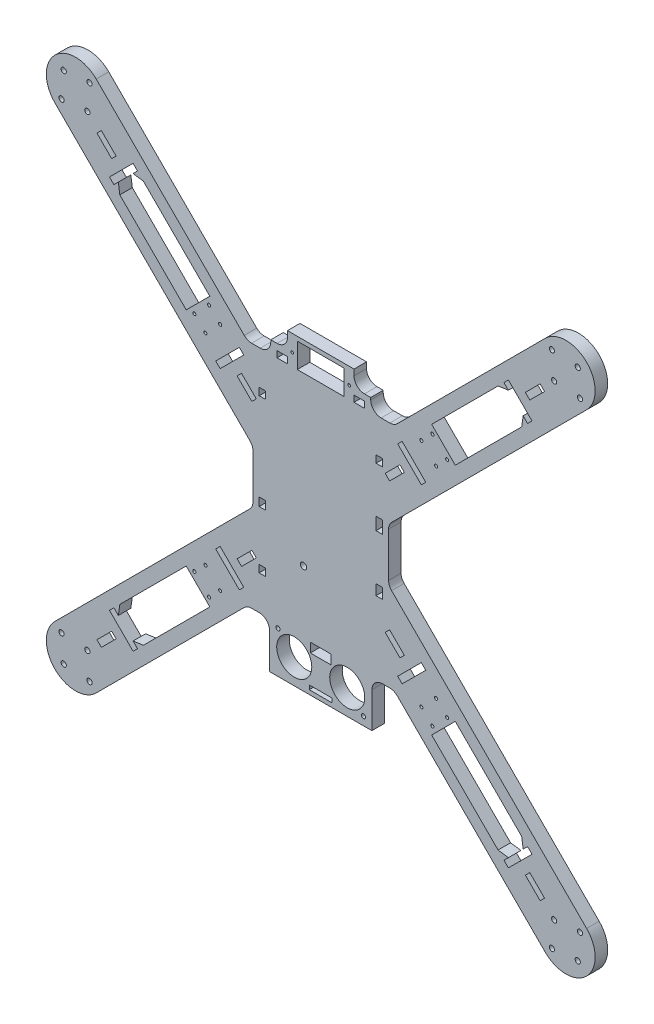
SolidWorks part; units mm, degrees
material "Custom Plastic"
ref_plane "Front Plane" through (0, 0, 0) normal (0, 0, 1) x (1, 0, 0)
ref_plane "Top Plane" through (0, 0, 0) normal (0, 1, 0) x (1, 0, 0)
ref_plane "Right Plane" through (0, 0, 0) normal (1, 0, 0) x (0, 0, -1)
sketch "Sketch1" plane through (0, 0, 0) normal (0, 0, 1) x (1, 0, 0)
  line L0 (117.5, 117.5) -> (-117.5, 117.5) construction
  line L1 (-117.5, 117.5) -> (117.5, -117.5) construction
  line L2 (117.5, -117.5) -> (-117.5, -117.5) construction
  line L3 (-117.5, -117.5) -> (117.5, 117.5) construction
  line L4 (117.5, 117.5) -> (117.5, -117.5) construction
  line L5 (-117.5, 117.5) -> (-117.5, -117.5) construction
  line L6 (0, 117.5) -> (0, -117.5) construction
  line L7 (35.201, 55) -> (15.95, 55)
  line L8 (-32.5, 55) -> (32.5, 55) construction
  line L9 (-35.201, 55) -> (-107.6005, 127.3995)
  line L10 (-127.3995, 107.6005) -> (-32.5, 12.701)
  line L11 (-117.5, 0) -> (117.5, 0) construction
  line L12 (-32.5, 12.701) -> (-32.5, -12.701)
  line L13 (32.5, 55) -> (32.5, -55) construction
  line L14 (32.5, -55) -> (-32.5, -55) construction
  line L15 (-32.5, -55) -> (-32.5, 55) construction
  line L16 (32.5, 55) -> (-32.5, -55) construction
  line L17 (-24.5, -55) -> (-24.5, -77)
  line L18 (-127.3995, -107.6005) -> (-32.5, -12.701)
  line L19 (-24.5, -77) -> (24.5, -77)
  line L20 (-35.201, -55) -> (-107.6005, -127.3995)
  line L21 (35.201, -55) -> (24.5, -55)
  line L22 (35.201, -55) -> (107.6005, -127.3995)
  line L23 (127.3995, -107.6005) -> (32.5, -12.701)
  line L24 (32.5, 12.701) -> (32.5, -12.701)
  line L25 (127.3995, 107.6005) -> (32.5, 12.701)
  line L26 (35.201, 55) -> (107.6005, 127.3995)
  line L27 (24.5, -55) -> (24.5, -77)
  line L28 (-24.5, -55) -> (-35.201, -55)
  line L29 (-15.95, 55) -> (-15.95, 68.8)
  line L30 (-15.95, 68.8) -> (15.95, 68.8)
  line L31 (15.95, 55) -> (15.95, 68.8)
  line L32 (-15.95, 55) -> (-35.201, 55)
  arc A0 (-107.6005, 127.3995) -> (-127.3995, 107.6005) centre (-117.5, 117.5) ccw
  arc A12 (-107.6005, -127.3995) -> (-127.3995, -107.6005) centre (-117.5, -117.5) cw
  arc A16 (107.6005, -127.3995) -> (127.3995, -107.6005) centre (117.5, -117.5) ccw
  arc A24 (107.6005, 127.3995) -> (127.3995, 107.6005) centre (117.5, 117.5) cw
  point P3 (0, 0)
  point P18 (0, 0)
  point P21 (0, -77)
  point P26 (0, 68.8)
  point P33 (-117.5, 117.5)
  point P34 (-32.5, 0)
  point P65 (0, -55)
  point P80 (0, 55)
  dimension "D3" = 14
  dimension "D8" = 24.5
  dimension "D7" = 22
  dimension "D1" = 235
  dimension "D2" = 235
  dimension "D4" = 65
  dimension "D5" = 110
  dimension "D6" = 28
  dimension "D9" = 13.8
  dimension "D10" = 31.9
extrude "Boss-Extrude1" add sketch "Sketch1" against normal blind 6
sketch "Sketch4" plane through (0, 0, 0) normal (0, 0, 1) x (1, 0, 0)
  line L0 (0, 0) -> (0, 55) construction
  line L2 (0, 0) -> (-32.5, 0) construction
  line L3 (-32.5, 12.701) -> (-32.5, -12.701) construction
  line L4 (-32.5, 0) -> (-32.5, 12.701) construction
  line L5 (-32.5, 12.701) -> (-127.3995, 107.6005) construction
  line L6 (-35.201, 55) -> (-107.6005, 127.3995) construction
  line L7 (-107.6005, 127.3995) -> (-127.3995, 107.6005) construction
  line L8 (-110.7825, 124.2175) -> (-124.2175, 110.7825) construction
  line L9 (-123.1569, 123.1569) -> (-111.8431, 111.8431) construction
  circle A20 centre (-110.7825, 124.2175) radius 1.25
  circle A21 centre (-124.2175, 110.7825) radius 1.25
  circle A22 centre (-123.1569, 123.1569) radius 1.25
  circle A23 centre (-111.8431, 111.8431) radius 1.25
  circle A24 centre (111.8431, 111.8431) radius 1.25
  circle A25 centre (110.7825, 124.2175) radius 1.25
  circle A26 centre (123.1569, 123.1569) radius 1.25
  circle A27 centre (124.2175, 110.7825) radius 1.25
  circle A28 centre (111.8431, -111.8431) radius 1.25
  circle A29 centre (124.2175, -110.7825) radius 1.25
  circle A30 centre (123.1569, -123.1569) radius 1.25
  circle A31 centre (110.7825, -124.2175) radius 1.25
  circle A32 centre (-111.8431, -111.8431) radius 1.25
  circle A33 centre (-110.7825, -124.2175) radius 1.25
  circle A34 centre (-123.1569, -123.1569) radius 1.25
  circle A35 centre (-124.2175, -110.7825) radius 1.25
  point P16 (-117.5, 117.5)
  point P19 (-117.5, 117.5)
  point P26 (-117.5, 117.5)
  point P62 (0, 0)
  dimension "D1" = 55
  dimension "D4" = 2.5
  dimension "D2" = 19
  dimension "D5" = 35.201
  dimension "D3" = 16
extrude "Cut-Extrude1" cut sketch "Sketch4" against normal through all
sketch "Sketch5" plane through (0, 0, 0) normal (0, 0, 1) x (1, 0, 0)
  line L4 (0, 0) -> (0, 14.0392) construction
  line L6 (15.95, 68.8) -> (-15.95, 68.8) construction
  line L7 (-11.25, 66.8) -> (-11.25, 55)
  line L8 (-11.25, 55) -> (11.25, 55)
  line L9 (11.25, 55) -> (11.25, 66.8)
  line L10 (11.25, 66.8) -> (-11.25, 66.8)
  line L12 (0, 66.8) -> (0, 55) construction
  line L13 (-13.65, 60.9) -> (13.65, 60.9) construction
  circle A2 centre (-13.65, 60.9) radius 0.65
  circle A3 centre (13.65, 60.9) radius 0.65
  point P20 (0, 60.9)
  point P21 (0, 60.9)
  dimension "D8" = 1.3
  dimension "D9" = 1.3
  dimension "D2" = 2
  dimension "D10" = 27.3
  dimension "D11" = 22.5
  dimension "D12" = 11.8
extrude "Cut-Extrude2" cut sketch "Sketch5" against normal through all
sketch "Sketch6" plane through (0, 0, 0) normal (0, 0, 1) x (1, 0, 0)
  line L1 (-11.25, 55) -> (11.25, 55) construction
  circle A0 centre (-8.25, -25) radius 1.5
  dimension "D3" = 3
  dimension "D1" = 80
  dimension "D2" = 3
extrude "Cut-Extrude3" cut sketch "Sketch6" against normal through all
sketch "Sketch7" plane through (0, 0, 0) normal (0, 0, 1) x (1, 0, 0)
  line L0 (-22.5, -55) -> (-22.5, -75) construction
  line L5 (-22.5, -75) -> (22.5, -75) construction
  line L6 (22.5, -75) -> (22.5, -55) construction
  line L7 (22.5, -55) -> (-22.5, -55) construction
  line L8 (0, -55) -> (0, -75) construction
  line L9 (-12.7, -65) -> (0, -65) construction
  line L10 (-24.5, -77) -> (24.5, -77) construction
  line L11 (-24.5, -55) -> (-24.5, -77) construction
  line L12 (-5, -55) -> (-5, -59.5)
  line L13 (-5, -59.5) -> (5, -59.5)
  line L15 (5, -55) -> (-5, -55)
  line L16 (-5.5, -75) -> (-5.5, -73)
  line L17 (-5.5, -73) -> (5.5, -73)
  line L21 (5.5, -75) -> (-5.5, -75)
  line L22 (5, -55) -> (5, -59.5)
  line L23 (5.5, -75) -> (5.5, -73)
  circle A5 centre (-20.5, -57) radius 1
  circle A6 centre (-12.7, -65) radius 8.4
  circle A7 centre (12.7, -65) radius 8.4
  circle A8 centre (20.5, -73) radius 1
  point P25 (0, -59.5)
  point P26 (0, -73)
  dimension "D3" = 2
  dimension "D6" = 20
  dimension "D13" = 5.5
  dimension "D5" = 45
  dimension "D1" = 2
  dimension "D4" = 16.8
  dimension "D14" = 2
  dimension "D2" = 2
  dimension "D7" = 2
  dimension "D8" = 2
  dimension "D9" = 12.7
  dimension "D10" = 5
  dimension "D11" = 4.5
  dimension "D12" = 2
  dimension "D15" = 2
  dimension "D16" = 2
extrude "Cut-Extrude4" cut sketch "Sketch7" against normal through all
sketch "Sketch8" plane through (0, 0, 0) normal (0, 0, 1) x (1, 0, 0)
  line L0 (101.2365, -89.9228) -> (89.9228, -101.2365)
  line L1 (89.9228, -101.2365) -> (87.8015, -99.1152)
  line L2 (36.8898, -48.2035) -> (48.2035, -36.8898)
  line L3 (48.2035, -36.8898) -> (50.3249, -39.0111)
  line L4 (105.4792, -85.6802) -> (85.6802, -105.4792) construction
  line L5 (127.3995, -107.6005) -> (32.5, -12.701) construction
  line L6 (35.201, -55) -> (107.6005, -127.3995) construction
  line L7 (40.0718, -37.9505) -> (37.9505, -40.0718)
  line L8 (115.8431, -107.8431) -> (111.8431, -111.8431) construction
  line L9 (37.9505, -40.0718) -> (30.8794, -33.0007)
  line L10 (50.3249, 39.0111) -> (48.2035, 36.8898)
  line L11 (30.8794, -33.0007) -> (33.0007, -30.8794)
  line L12 (33.0007, -30.8794) -> (40.0718, -37.9505)
  line L13 (42.5467, -42.5467) -> (39.0111, -39.0111) construction
  line L14 (35.201, -55) -> (107.6005, -127.3995) construction
  line L15 (100.1759, -98.0546) -> (98.0546, -100.1759)
  line L16 (98.0546, -100.1759) -> (105.1256, -107.247)
  line L17 (105.1256, -107.247) -> (107.247, -105.1256)
  line L18 (107.247, -105.1256) -> (100.1759, -98.0546)
  line L19 (99.1152, -99.1152) -> (95.5797, -95.5797) construction
  line L20 (-101.2365, -89.9228) -> (-99.1152, -87.8015)
  line L21 (-100.1759, -98.0546) -> (-107.247, -105.1256)
  line L22 (-107.247, -105.1256) -> (-105.1256, -107.247)
  line L23 (-105.1256, -107.247) -> (-98.0546, -100.1759)
  line L24 (-98.0546, -100.1759) -> (-100.1759, -98.0546)
  line L25 (-89.9228, -101.2365) -> (-101.2365, -89.9228)
  line L26 (-36.8898, -48.2035) -> (-39.0111, -50.3249)
  line L27 (-48.2035, -36.8898) -> (-36.8898, -48.2035)
  line L28 (-37.9505, -40.0718) -> (-40.0718, -37.9505)
  line L29 (-30.8794, -33.0007) -> (-37.9505, -40.0718)
  line L30 (-40.0718, -37.9505) -> (-33.0007, -30.8794)
  line L31 (-33.0007, -30.8794) -> (-30.8794, -33.0007)
  line L32 (-89.9228, 101.2365) -> (-87.8015, 99.1152)
  line L33 (-98.0546, 100.1759) -> (-105.1256, 107.247)
  line L34 (-105.1256, 107.247) -> (-107.247, 105.1256)
  line L35 (-107.247, 105.1256) -> (-100.1759, 98.0546)
  line L36 (-100.1759, 98.0546) -> (-98.0546, 100.1759)
  line L37 (-101.2365, 89.9228) -> (-89.9228, 101.2365)
  line L38 (-48.2035, 36.8898) -> (-50.3249, 39.0111)
  line L39 (-36.8898, 48.2035) -> (-48.2035, 36.8898)
  line L40 (-40.0718, 37.9505) -> (-37.9505, 40.0718)
  line L41 (-33.0007, 30.8794) -> (-40.0718, 37.9505)
  line L42 (-37.9505, 40.0718) -> (-30.8794, 33.0007)
  line L43 (-30.8794, 33.0007) -> (-33.0007, 30.8794)
  line L44 (101.2365, 89.9228) -> (99.1152, 87.8015)
  line L45 (100.1759, 98.0546) -> (107.247, 105.1256)
  line L46 (107.247, 105.1256) -> (105.1256, 107.247)
  line L47 (105.1256, 107.247) -> (98.0546, 100.1759)
  line L48 (98.0546, 100.1759) -> (100.1759, 98.0546)
  line L49 (89.9228, 101.2365) -> (101.2365, 89.9228)
  line L50 (36.8898, 48.2035) -> (39.0111, 50.3249)
  line L51 (48.2035, 36.8898) -> (36.8898, 48.2035)
  line L52 (37.9505, 40.0718) -> (40.0718, 37.9505)
  line L53 (30.8794, 33.0007) -> (37.9505, 40.0718)
  line L54 (40.0718, 37.9505) -> (33.0007, 30.8794)
  line L55 (33.0007, 30.8794) -> (30.8794, 33.0007)
  line L56 (32.5, 12.701) -> (127.3995, 107.6005) construction
  line L57 (41.8396, 53.1533) -> (84.9731, 96.2868)
  line L58 (96.2868, 84.9731) -> (53.1533, 41.8396)
  line L59 (87.8015, 99.1152) -> (89.9228, 101.2365)
  line L60 (99.1152, -87.8015) -> (96.9939, -89.9228)
  line L61 (-96.2868, -84.9731) -> (-53.1533, -41.8396)
  line L62 (96.9939, -89.9228) -> (96.2868, -84.9731)
  line L63 (99.1152, -87.8015) -> (101.2365, -89.9228)
  line L64 (87.8015, -99.1152) -> (89.9228, -96.9939)
  line L65 (-87.8015, -99.1152) -> (-89.9228, -101.2365)
  line L66 (89.9228, -96.9939) -> (84.9731, -96.2868)
  line L67 (84.9731, -96.2868) -> (41.8396, -53.1533)
  line L70 (53.1533, -41.8396) -> (96.2868, -84.9731)
  line L73 (39.0111, -50.3249) -> (36.8898, -48.2035)
  line L74 (-89.9228, -96.9939) -> (-84.9731, -96.2868)
  line L75 (-87.8015, -99.1152) -> (-89.9228, -96.9939)
  line L76 (-96.9939, -89.9228) -> (-96.2868, -84.9731)
  line L77 (-99.1152, -87.8015) -> (-96.9939, -89.9228)
  line L82 (-96.9939, 89.9228) -> (-96.2868, 84.9731)
  line L83 (-99.1152, 87.8015) -> (-96.9939, 89.9228)
  line L84 (-89.9228, 96.9939) -> (-84.9731, 96.2868)
  line L85 (-87.8015, 99.1152) -> (-89.9228, 96.9939)
  line L90 (89.9228, 96.9939) -> (84.9731, 96.2868)
  line L91 (87.8015, 99.1152) -> (89.9228, 96.9939)
  line L92 (96.9939, 89.9228) -> (96.2868, 84.9731)
  line L93 (99.1152, 87.8015) -> (96.9939, 89.9228)
  line L98 (-39.0111, 50.3249) -> (-36.8898, 48.2035)
  line L99 (-53.1533, 41.8396) -> (-96.2868, 84.9731)
  line L100 (-99.1152, 87.8015) -> (-101.2365, 89.9228)
  line L101 (-84.9731, 96.2868) -> (-41.8396, 53.1533)
  line L102 (-41.8396, -53.1533) -> (-84.9731, -96.2868)
  line L103 (-50.3249, -39.0111) -> (-48.2035, -36.8898)
  line L104 (96.2868, 84.9731) -> (84.9731, 96.2868) construction
  line L105 (-39.0111, -50.3249) -> (-41.8396, -53.1533)
  line L106 (41.8396, -53.1533) -> (39.0111, -50.3249)
  line L107 (53.1533, -41.8396) -> (50.3249, -39.0111)
  line L108 (41.8396, 53.1533) -> (39.0111, 50.3249)
  line L109 (53.1533, 41.8396) -> (50.3249, 39.0111)
  line L110 (-50.3249, -39.0111) -> (-53.1533, -41.8396)
  line L111 (-50.3249, 39.0111) -> (-53.1533, 41.8396)
  line L112 (-39.0111, 50.3249) -> (-41.8396, 53.1533)
  point P10 (95.5797, -95.5797)
  point P11 (95.5797, -95.5797)
  point P68 (0, 0)
  point P122 (0, 0)
  dimension "D1" = 23
  dimension "D2" = 75
  dimension "D3" = 3
  dimension "D4" = 10
  dimension "D5" = 5
  dimension "D6" = 6
  dimension "D7" = 3
  dimension "D8" = 10
  dimension "D9" = 5
  dimension "D11" = 6
  dimension "D12" = 3
  dimension "D13" = 4
  dimension "D14" = 3
  dimension "D15" = 3
  dimension "D16" = 4
  dimension "D17" = 3
  dimension "D22" = 4
  dimension "D24" = 3
  dimension "D25" = 4
  dimension "D28" = 3
  dimension "D29" = 3
  dimension "D30" = 4
  dimension "D31" = 4
  dimension "D38" = 4
  dimension "D40" = 3
  dimension "D41" = 3
  dimension "D42" = 4
  dimension "D43" = 4
  dimension "D10" = 4
extrude "Cut-Extrude5" cut sketch "Sketch8" against normal through all
sketch "Sketch9" plane through (-5.6569, 5.6569, 0) normal (0.7071, -0.7071, 0) x (0, 0, -1)
  line L0 (6, 128.1701) -> (6, 60.1701) construction
  line L1 (6, 83.1701) -> (0, 83.1701)
  line L2 (6, 83.1701) -> (6, 63.1701)
  line L3 (6, 63.1701) -> (0, 63.1701)
  line L4 (0, 83.1701) -> (0, 63.1701)
  line L5 (0, 128.1701) -> (0, 60.1701) construction
  line L6 (0, 0) -> (28.0274, 0) construction
  dimension "D1" = 3
  dimension "D2" = 20
extrude "Boss-Extrude2" add sketch "Sketch9" along normal up to next
sketch "Sketch11" plane through (5.6569, 5.6569, 0) normal (-0.7071, -0.7071, 0) x (0, 0, 1)
  line L0 (-6, -128.1701) -> (-6, -60.1701) construction
  line L1 (-6, -63.1701) -> (0, -63.1701)
  line L2 (-6, -63.1701) -> (-6, -83.1701)
  line L3 (-6, -83.1701) -> (0, -83.1701)
  line L4 (0, -63.1701) -> (0, -83.1701)
  line L5 (0, -128.1701) -> (0, -60.1701) construction
  dimension "D1" = 3
  dimension "D2" = 20
extrude "Boss-Extrude3" add sketch "Sketch11" along normal up to next
sketch "Sketch12" plane through (5.6569, -5.6569, 0) normal (-0.7071, 0.7071, 0) x (0, 0, 1)
  line L0 (-6, -128.1701) -> (-6, -60.1701) construction
  line L1 (-6, -63.1701) -> (0, -63.1701)
  line L2 (-6, -63.1701) -> (-6, -83.1701)
  line L3 (-6, -83.1701) -> (0, -83.1701)
  line L4 (0, -63.1701) -> (0, -83.1701)
  line L5 (0, -128.1701) -> (0, -60.1701) construction
  point P11 (-6, -60.1701)
  dimension "D1" = 3
  dimension "D2" = 20
extrude "Boss-Extrude4" add sketch "Sketch12" along normal up to next
sketch "Sketch13" plane through (5.6569, 5.6569, 0) normal (-0.7071, -0.7071, 0) x (0, 0, 1)
  line L0 (-6, 60.1701) -> (-6, 128.1701) construction
  line L1 (-6, 63.1701) -> (0, 63.1701)
  line L2 (-6, 63.1701) -> (-6, 83.1701)
  line L3 (-6, 83.1701) -> (0, 83.1701)
  line L4 (0, 63.1701) -> (0, 83.1701)
  line L5 (0, 60.1701) -> (0, 128.1701) construction
  point P11 (-6, 60.1701)
  dimension "D1" = 3
  dimension "D2" = 20
extrude "Boss-Extrude5" add sketch "Sketch13" along normal up to next
sketch "Sketch14" plane through (0, 0, -6) normal (0, 0, -1) x (-1, 0, 0)
  line L0 (32.5, 0) -> (-32.5, 0) construction
  line L1 (32.5, 12.701) -> (32.5, -12.701) construction
  line L2 (-32.5, -12.701) -> (-32.5, 12.701) construction
  line L3 (28, -38.5) -> (28, 38.5) construction
  line L14 (-26.5, 13) -> (-26.5, 7)
  line L17 (-26.5, 7) -> (-29.5, 7)
  line L19 (-26.5, 13) -> (-29.5, 13)
  line L23 (26.5, -38.5) -> (29.5, -38.5)
  line L24 (26.5, -38.5) -> (26.5, -35)
  line L25 (26.5, -35) -> (29.5, -35)
  line L26 (29.5, -38.5) -> (29.5, -35)
  line L27 (26.5, -11) -> (29.5, -11)
  line L28 (26.5, -11) -> (26.5, -7)
  line L29 (26.5, -7) -> (29.5, -7)
  line L30 (29.5, -11) -> (29.5, -7)
  line L31 (26.5, 35) -> (29.5, 35)
  line L32 (26.5, 35) -> (26.5, 38.5)
  line L33 (26.5, 38.5) -> (29.5, 38.5)
  line L34 (29.5, 35) -> (29.5, 38.5)
  line L35 (-29.5, 13) -> (-29.5, 7)
  line L36 (32.5, 12.701) -> (32.5, -12.701) construction
  line L37 (-26.5, -20) -> (-29.5, -20)
  line L38 (-26.5, -20) -> (-26.5, -15)
  line L39 (-26.5, -15) -> (-29.5, -15)
  line L40 (-29.5, -20) -> (-29.5, -15)
  line L41 (-26.5, 35) -> (-29.5, 35)
  line L42 (-26.5, 35) -> (-26.5, 38.5)
  line L43 (-26.5, 38.5) -> (-29.5, 38.5)
  line L44 (-29.5, 35) -> (-29.5, 38.5)
  line L45 (-32.5, -12.701) -> (-32.5, 12.701) construction
  point P11 (28, -38.5)
  point P16 (28, 0)
  point P28 (-28, 13)
  point P38 (-28, 7)
  dimension "D2" = 3
  dimension "D3" = 3.5
  dimension "D4" = 24
  dimension "D5" = 7
  dimension "D6" = 22
  dimension "D7" = 6
  dimension "D8" = 3.5
  dimension "D9" = 22
  dimension "D10" = 4
  dimension "D11" = 3.5
  dimension "D12" = 42
  dimension "D13" = 5
  dimension "D14" = 3
  dimension "D15" = 3
  dimension "D16" = 3
  dimension "D17" = 7
extrude "Cut-Extrude6" cut sketch "Sketch14" against normal through all
sketch "Sketch15" plane through (0, 0, -6) normal (0, 0, -1) x (-1, 0, 0)
  line L0 (-55.2746, -48.2035) -> (-48.2035, -55.2746) construction
  line L1 (-48.2035, -55.2746) -> (-53.5068, -60.5779) construction
  line L2 (-53.5068, -60.5779) -> (-60.5779, -53.5068) construction
  line L3 (-60.5779, -53.5068) -> (-55.2746, -48.2035) construction
  line L4 (-64.2902, -44.4912) -> (-44.4912, -64.2902) construction
  line L5 (-127.3995, -107.6005) -> (-32.5, -12.701) construction
  line L6 (-35.201, -55) -> (-107.6005, -127.3995) construction
  line L7 (-57.0424, -57.0424) -> (-51.7391, -51.7391) construction
  line L8 (-53.1533, -64.467) -> (-64.467, -53.1533) construction
  circle A6 centre (-60.5779, -53.5068) radius 0.75
  circle A7 centre (-55.2746, -48.2035) radius 0.75
  circle A8 centre (-48.2035, -55.2746) radius 0.75
  circle A9 centre (-53.5068, -60.5779) radius 0.75
  circle A10 centre (-53.5068, 60.5779) radius 0.75
  circle A11 centre (-48.2035, 55.2746) radius 0.75
  circle A12 centre (-60.5779, 53.5068) radius 0.75
  circle A13 centre (-55.2746, 48.2035) radius 0.75
  circle A14 centre (60.5779, 53.5068) radius 0.75
  circle A15 centre (55.2746, 48.2035) radius 0.75
  circle A16 centre (53.5068, 60.5779) radius 0.75
  circle A17 centre (48.2035, 55.2746) radius 0.75
  circle A18 centre (53.5068, -60.5779) radius 0.75
  circle A19 centre (48.2035, -55.2746) radius 0.75
  circle A20 centre (60.5779, -53.5068) radius 0.75
  circle A21 centre (55.2746, -48.2035) radius 0.75
  point P12 (-54.3907, -54.3907)
  point P19 (-54.3907, -54.3907)
  point P47 (0, 0)
  dimension "D3" = 1.5
  dimension "D1" = 7.5
  dimension "D2" = 10
  dimension "D4" = 2.5
  dimension "D5" = 4
extrude "Cut-Extrude7" cut sketch "Sketch15" against normal through all
sketch "Sketch17" plane through (0, 0, -6) normal (0, 0, -1) x (-1, 0, 0)
  line L0 (0, 68.8) -> (0, 41.1241) construction
  line L1 (15.95, 55) -> (23.95, 55)
  line L2 (15.95, 55) -> (15.95, 61)
  line L3 (15.95, 61) -> (23.95, 61)
  line L4 (23.95, 55) -> (23.95, 61)
  line L5 (-15.95, 68.8) -> (15.95, 68.8) construction
  line L6 (-15.95, 55) -> (-15.95, 58)
  line L7 (20.95, 55) -> (15.95, 55)
  line L10 (15.95, 55) -> (15.95, 58)
  line L11 (-20.95, 58) -> (-15.95, 58)
  line L12 (-20.95, 55) -> (-20.95, 58)
  line L13 (-20.95, 55) -> (-15.95, 55)
  line L14 (-23.95, 55) -> (-23.95, 61)
  line L15 (-15.95, 61) -> (-23.95, 61)
  line L16 (-15.95, 55) -> (-15.95, 61)
  line L17 (-15.95, 55) -> (-23.95, 55)
  dimension "D1" = 6
  dimension "D2" = 8
extrude "Boss-Extrude8" add sketch "Sketch17" against normal up to surface (6 mm away) contours L2 L3 L4 L1 | L16 L15 L14 L17 up to face at (47.4535, 55.2746, 0)
sketch "Sketch19" plane through (0, 0, -6) normal (0, 0, -1) x (-1, 0, 0)
  line L0 (15.95, 61) -> (23.95, 61) construction
  line L1 (20.95, 58) -> (15.95, 58)
  line L2 (20.95, 58) -> (20.95, 55)
  line L3 (20.95, 55) -> (15.95, 55)
  line L4 (15.95, 58) -> (15.95, 55)
  line L5 (23.95, 55) -> (23.95, 61) construction
  line L6 (0, 68.8) -> (0, 43.8944) construction
  line L7 (-15.95, 68.8) -> (15.95, 68.8) construction
  line L8 (-15.95, 58) -> (-15.95, 55)
  line L9 (-20.95, 55) -> (-15.95, 55)
  line L10 (-20.95, 58) -> (-20.95, 55)
  line L11 (-20.95, 58) -> (-15.95, 58)
  dimension "D1" = 5
  dimension "D2" = 3
  dimension "D3" = 3
  dimension "D4" = 3
extrude "Cut-Extrude9" cut sketch "Sketch19" against normal through all
fillet "Fillet1" radius 5 14 edges at (-32.5, -12.701, -3) (-32.5, 12.701, -3) (32.5, 12.701, -3) (32.5, -12.701, -3) (24.5, -55, -3) (35.201, -55, -3) (-24.5, -55, -3) (-35.201, -55, -3) (15.95, 61, -3) (23.95, 55, -3) (35.201, 55, -3) (-15.95, 61, -3) (-23.95, 55, -3) (-35.201, 55, -3)
